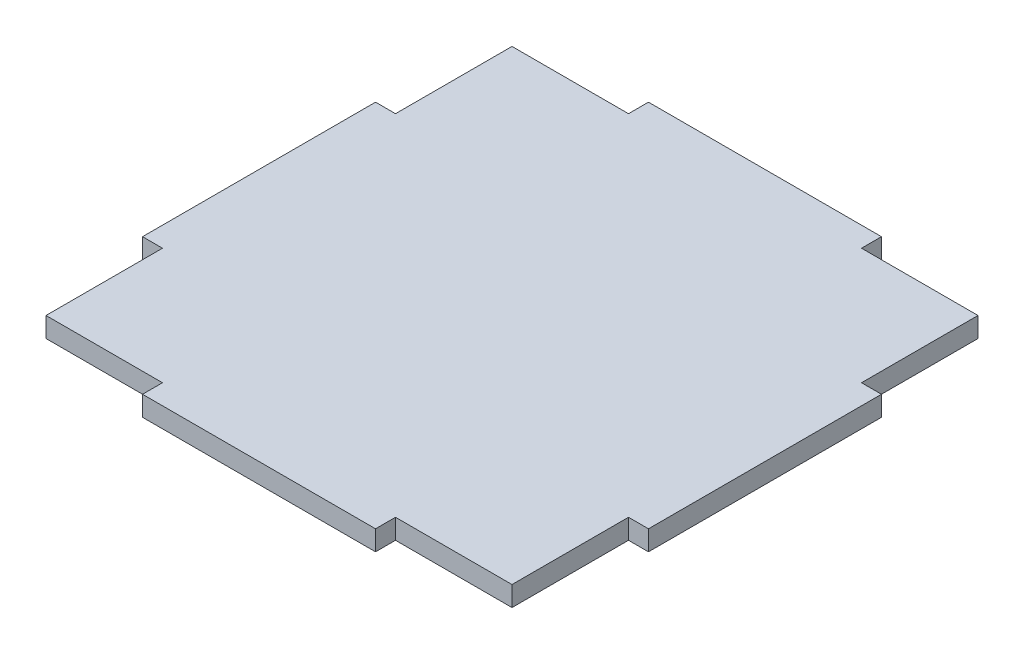
SolidWorks part; units mm, degrees
ref_plane "Front Plane" through (0, 0, 0) normal (0, 0, 1) x (1, 0, 0)
ref_plane "Top Plane" through (0, 0, 0) normal (0, 1, 0) x (1, 0, 0)
ref_plane "Right Plane" through (0, 0, 0) normal (1, 0, 0) x (0, 0, -1)
sketch "Sketch1" plane through (0, 0, 0) normal (0, 1, 0) x (1, 0, 0)
  line L0 (0, 35) -> (0, -35) construction
  line L1 (-35, -35) -> (-17.5, -35)
  line L2 (-35, -35) -> (-35, -17.5)
  line L3 (-35, 35) -> (-17.5, 35)
  line L4 (35, -35) -> (35, -17.5)
  line L5 (-35, -35) -> (35, 35) construction
  line L6 (-35, 35) -> (35, -35) construction
  line L11 (-38, -38) -> (38, 38) construction
  line L12 (-38, 38) -> (38, -38) construction
  line L13 (-35, 0) -> (35, 0) construction
  line L14 (-17.5, 38) -> (-17.5, 35)
  line L15 (-38, 17.5) -> (-35, 17.5)
  line L16 (17.5, 38) -> (17.5, 35)
  line L17 (-38, -17.5) -> (-35, -17.5)
  line L18 (38, 17.5) -> (35, 17.5)
  line L19 (38, -17.5) -> (35, -17.5)
  line L20 (17.5, -38) -> (17.5, -35)
  line L21 (-17.5, -38) -> (-17.5, -35)
  line L22 (-38, -17.5) -> (-38, 17.5)
  line L23 (38, 17.5) -> (38, -17.5)
  line L24 (-17.5, -38) -> (17.5, -38)
  line L25 (-17.5, 38) -> (17.5, 38)
  line L26 (17.5, 35) -> (35, 35)
  line L27 (35, 17.5) -> (35, 35)
  line L28 (17.5, -35) -> (35, -35)
  line L29 (-35, 17.5) -> (-35, 35)
  point P0 (0, 0)
  point P6 (0, 0)
  dimension "D1" = 76
  dimension "D2" = 70
  dimension "D3" = 76
  dimension "D4" = 70
  dimension "D5" = 17.5
  dimension "D6" = 17.5
  dimension "D7" = 3
  dimension "D8" = 3
extrude "Boss-Extrude1" add sketch "Sketch1" along normal blind 3
